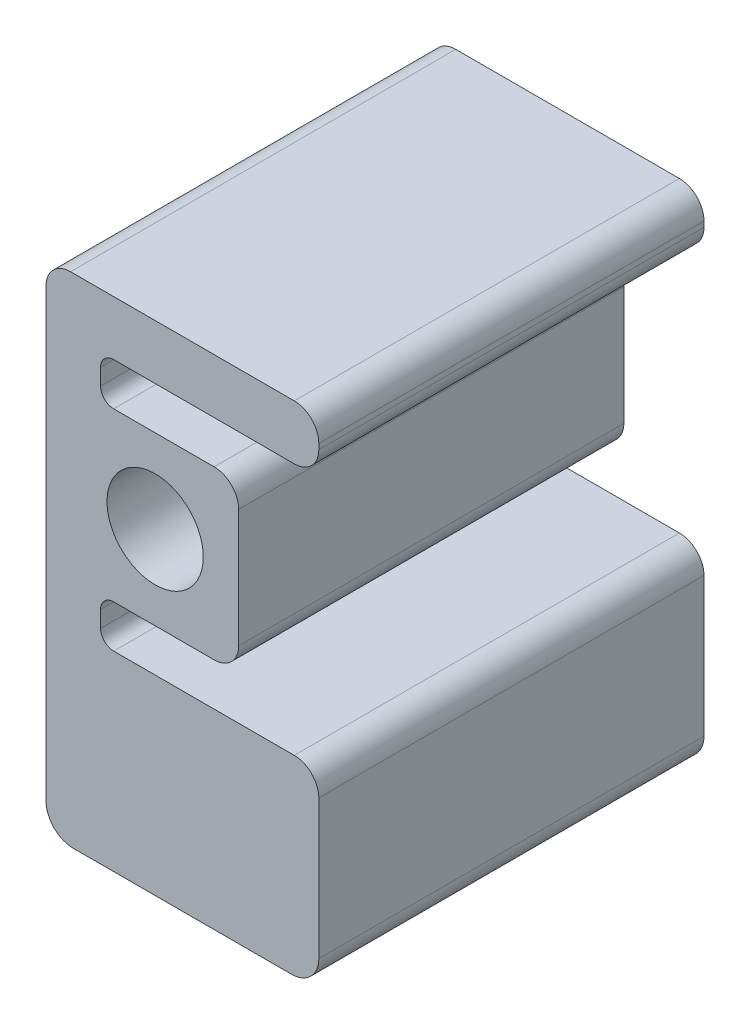
SolidWorks part; units mm, degrees
material "Pink Foam"
ref_plane "Front Plane" through (0, 0, 0) normal (0, 0, 1) x (1, 0, 0)
ref_plane "Top Plane" through (0, 0, 0) normal (0, 1, 0) x (1, 0, 0)
ref_plane "Right Plane" through (0, 0, 0) normal (1, 0, 0) x (0, 0, -1)
sketch "Sketch1" plane through (0, 0, 0) normal (0, 0, 1) x (1, 0, 0)
  line L0 (-25.4, -67.48) -> (-25.4, 36.365)
  line L2 (38.1, -67.48) -> (38.1, -35.095)
  line L3 (32.385, -29.38) -> (-9.652, -29.38)
  line L4 (-12.7, -26.332) -> (-12.7, -22.503)
  line L5 (-9.652, -19.455) -> (0, -19.455)
  line L6 (-9.652, 19.455) -> (0, 19.455)
  line L7 (-12.7, 22.503) -> (-12.7, 26.332)
  line L8 (-9.652, 29.38) -> (32.385, 29.38)
  line L9 (38.1, 35.095) -> (38.1, 36.365)
  line L10 (32.385, 42.08) -> (-19.685, 42.08)
  line L15 (0, -11.2) -> (0, -19.455) construction
  line L16 (0, 11.2) -> (0, 19.455) construction
  line L17 (11.2, 0) -> (19.455, 0) construction
  line L18 (0, 19.455) -> (13.74, 19.455)
  line L19 (19.455, 13.74) -> (19.455, 0)
  line L20 (19.455, 0) -> (19.455, -13.74)
  line L21 (13.74, -19.455) -> (0, -19.455)
  line L24 (31.75, -73.83) -> (-19.05, -73.83)
  circle A0 centre (0, 0) radius 11.2
  arc A3 (-19.685, 42.08) -> (-25.4, 36.365) centre (-19.685, 36.365) ccw
  arc A4 (38.1, 36.365) -> (32.385, 42.08) centre (32.385, 36.365) ccw
  arc A6 (32.385, 29.38) -> (38.1, 35.095) centre (32.385, 35.095) ccw
  arc A7 (38.1, -35.095) -> (32.385, -29.38) centre (32.385, -35.095) ccw
  arc A8 (19.455, -13.74) -> (13.74, -19.455) centre (13.74, -13.74) cw
  arc A9 (13.74, 19.455) -> (19.455, 13.74) centre (13.74, 13.74) cw
  arc A10 (-12.7, 26.332) -> (-9.652, 29.38) centre (-9.652, 26.332) cw
  arc A11 (-9.652, 19.455) -> (-12.7, 22.503) centre (-9.652, 22.503) cw
  arc A12 (-12.7, -22.503) -> (-9.652, -19.455) centre (-9.652, -22.503) cw
  arc A13 (-9.652, -29.38) -> (-12.7, -26.332) centre (-9.652, -26.332) cw
  arc A14 (31.75, -73.83) -> (38.1, -67.48) centre (31.75, -67.48) ccw
  arc A15 (-19.05, -73.83) -> (-25.4, -67.48) centre (-19.05, -67.48) cw
  point P3 (0, 0)
  point P4 (0, 0)
  point P6 (0, 0)
  point P12 (0, 11.2)
  point P18 (-25.4, -72.8366)
  point P19 (0, 0)
  point P20 (0, -11.2)
  point P22 (11.2, 0)
  point P23 (38.1, -73.83)
  point P32 (0, 0)
  point P33 (38.1, -74.3693)
  point P45 (-12.7, 29.38)
  point P48 (-12.7, 19.455)
  point P53 (-12.7, -29.38)
  point P54 (-25.4, -73.83)
  point P55 (0, 0)
  point P57 (38.1, -73.83)
  point P60 (38.1, -73.83)
  point P63 (-25.4, -73.83)
  dimension "D1" = 22.4
  dimension "D11" = 3.048
  dimension "D9" = 5.715
  dimension "D14" = 5.715
  dimension "D12" = 6.35
  dimension "D2" = 25.4
  dimension "D3" = 8.255
  dimension "D4" = 9.925
  dimension "D5" = 44.45
  dimension "D6" = 9.925
  dimension "D7" = 12.7
  dimension "D8" = 12.7
  dimension "D10" = 63.5
extrude "Boss-Extrude1" add sketch "Sketch1" along normal blind 89.6518
